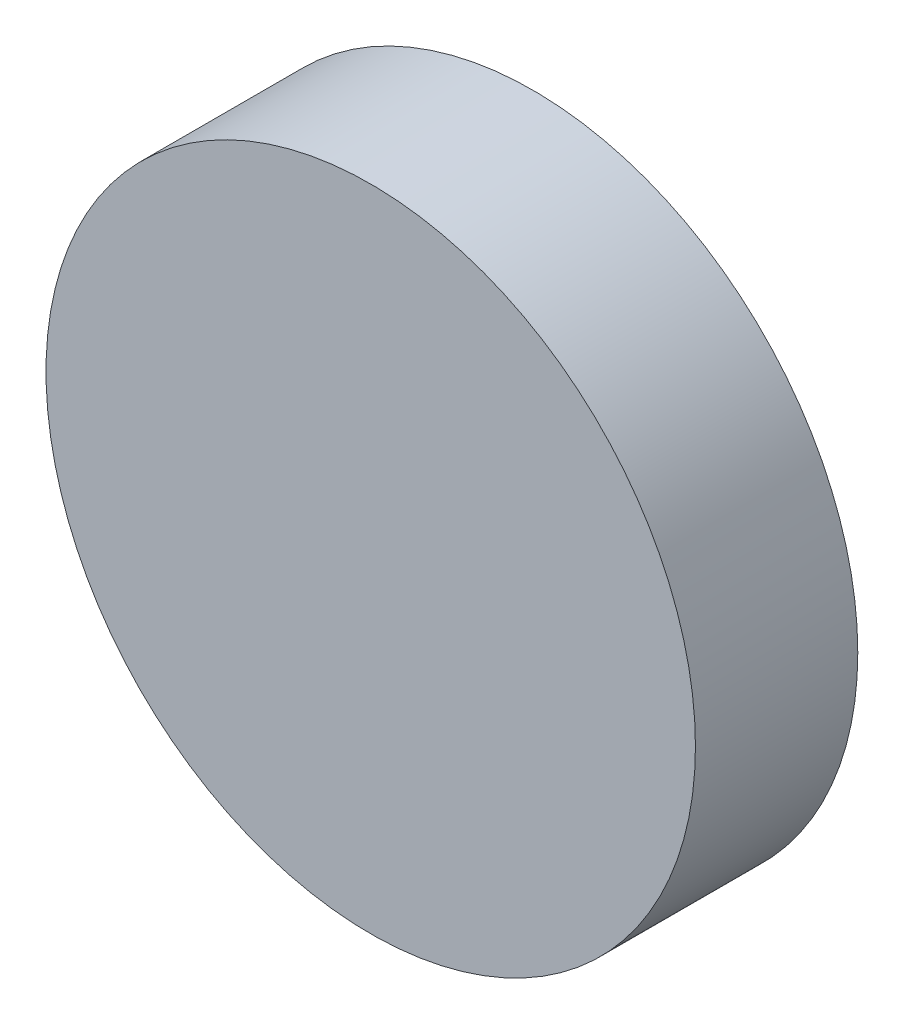
SolidWorks part; units mm, degrees
ref_plane "Front Plane" through (0, 0, 0) normal (0, 0, 1) x (1, 0, 0)
ref_plane "Top Plane" through (0, 0, 0) normal (0, 1, 0) x (1, 0, 0)
ref_plane "Right Plane" through (0, 0, 0) normal (1, 0, 0) x (0, 0, -1)
sketch "Sketch1" plane through (0, 0, 0) normal (0, 0, 1) x (1, 0, 0)
  circle A0 centre (0, 0) radius 3.175
  dimension "D1" = 6.35
extrude "Boss-Extrude1" add sketch "Sketch1" along normal blind 1.5875
